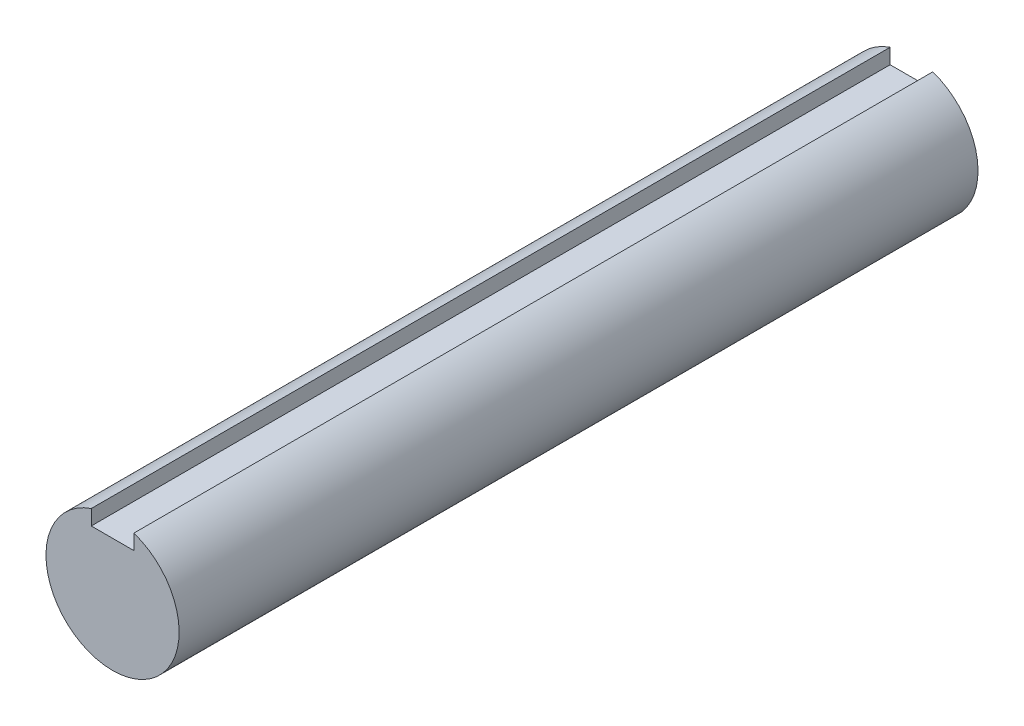
SolidWorks part; units mm, degrees
ref_plane "Front Plane" through (0, 0, 0) normal (0, 0, 1) x (1, 0, 0)
ref_plane "Top Plane" through (0, 0, 0) normal (0, 1, 0) x (1, 0, 0)
ref_plane "Right Plane" through (0, 0, 0) normal (1, 0, 0) x (0, 0, -1)
sketch "Sketch1" plane through (0, 0, 0) normal (0, 0, 1) x (1, 0, 0)
  line L1 (-4, 9) -> (4, 9)
  line L2 (-4, 9) -> (-4, 16)
  line L3 (-4, 16) -> (4, 16)
  line L4 (4, 9) -> (4, 16)
  line L5 (-4, 9) -> (4, 16) construction
  line L6 (-4, 16) -> (4, 9) construction
  circle A0 centre (0, 0) radius 12.5
  point P3 (0, 12.5)
  dimension "D1" = 25
  dimension "D2" = 8
  dimension "D3" = 7
extrude "Boss-Extrude1" add sketch "Sketch1" along normal blind 150 contours L2 A0 L4 L1
